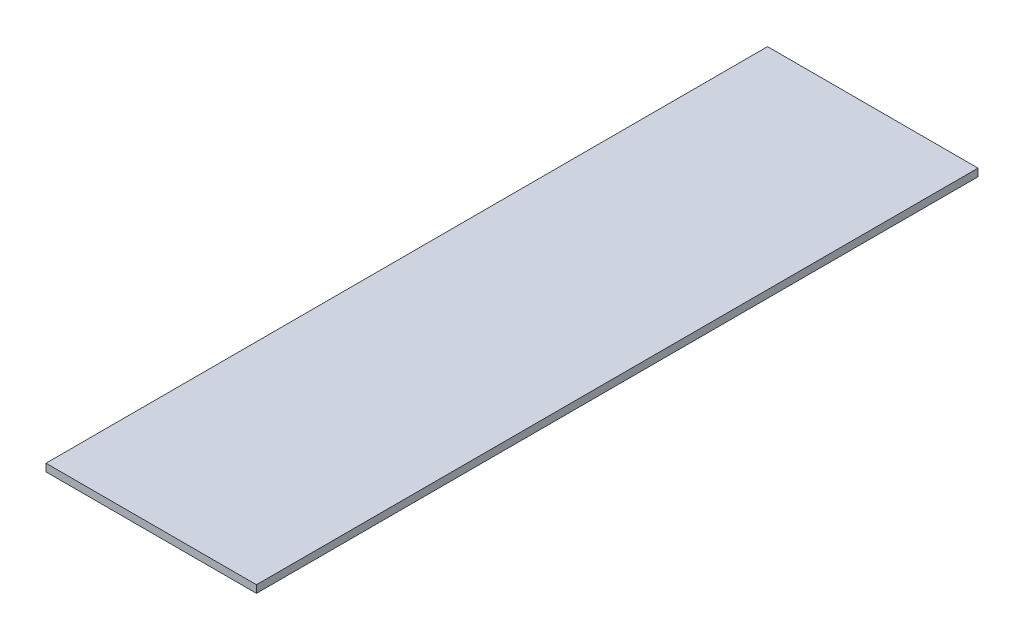
SolidWorks part; units mm, degrees
material "Pine"
ref_plane "Front Plane" through (0, 0, 0) normal (0, 0, 1) x (1, 0, 0)
ref_plane "Top Plane" through (0, 0, 0) normal (0, 1, 0) x (1, 0, 0)
ref_plane "Right Plane" through (0, 0, 0) normal (1, 0, 0) x (0, 0, -1)
sketch "Sketch1" plane through (0, 0, 0) normal (0, 1, 0) x (1, 0, 0)
  line L0 (-177.8, 0) -> (177.8, 0) construction
  line L1 (-177.8, 939.8) -> (177.8, 939.8)
  line L2 (-177.8, 939.8) -> (-177.8, -279.4)
  line L3 (-177.8, -279.4) -> (177.8, -279.4)
  line L4 (177.8, 939.8) -> (177.8, -279.4)
  dimension "D1" = 1219.2
  dimension "D2" = 279.4
  dimension "D3" = 355.6
extrude "Boss-Extrude1" add sketch "Sketch1" against normal blind 12.7
